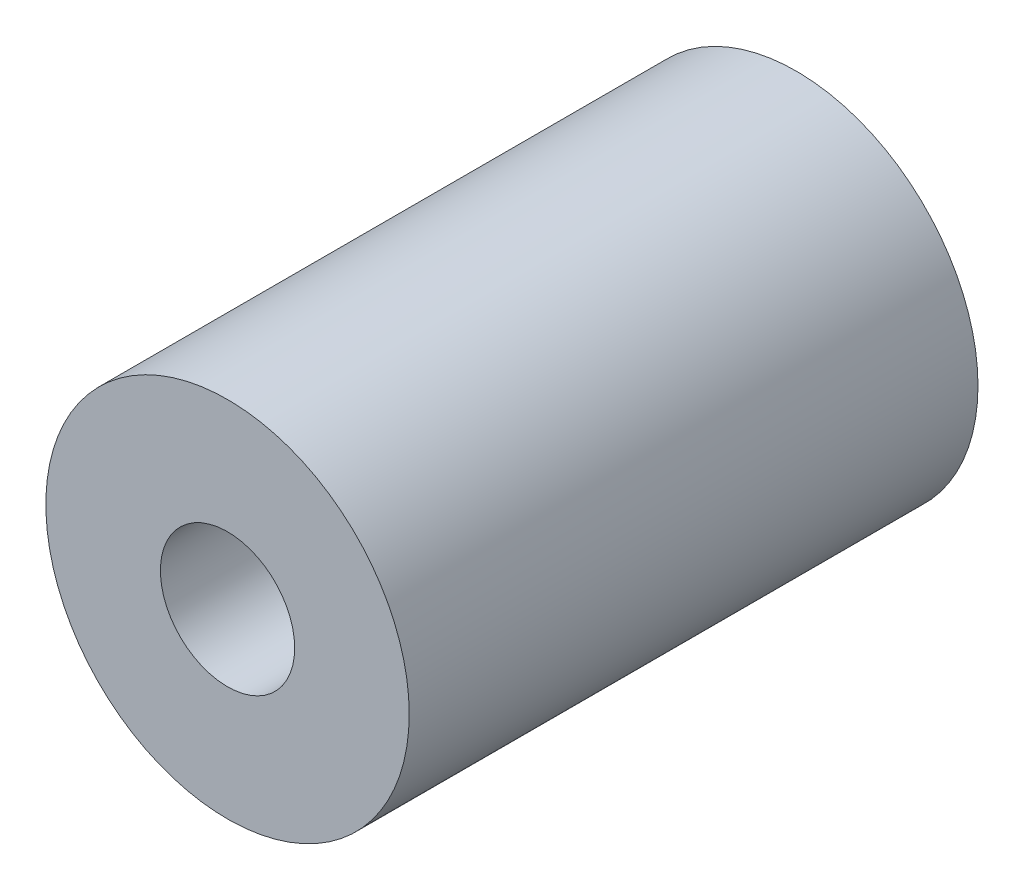
SolidWorks part; units mm, degrees
ref_plane "Front Plane" through (0, 0, 0) normal (0, 0, 1) x (1, 0, 0)
ref_plane "Top Plane" through (0, 0, 0) normal (0, 1, 0) x (1, 0, 0)
ref_plane "Right Plane" through (0, 0, 0) normal (1, 0, 0) x (0, 0, -1)
sketch "Sketch1" plane through (0, 0, 0) normal (0, 0, 1) x (1, 0, 0)
  circle A0 centre (0, 0) radius 0.85
  circle A1 centre (0, 0) radius 2.3
  dimension "D1" = 4.6
  dimension "D2" = 1.7
extrude "Boss-Extrude1" add sketch "Sketch1" along normal blind 7.2
